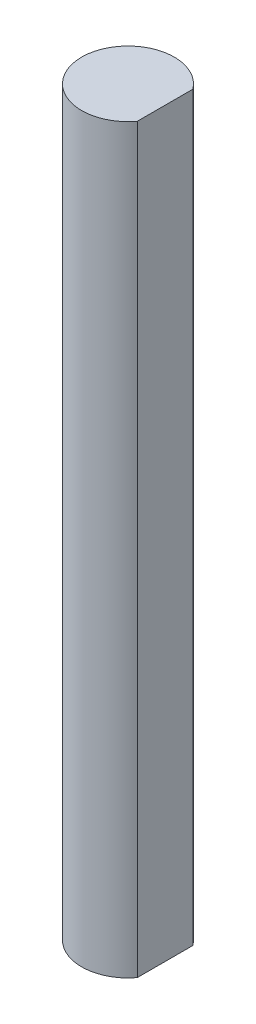
SolidWorks part; units mm, degrees
ref_plane "Front Plane" through (0, 0, 0) normal (0, 0, 1) x (1, 0, 0)
ref_plane "Top Plane" through (0, 0, 0) normal (0, 1, 0) x (1, 0, 0)
ref_plane "Right Plane" through (0, 0, 0) normal (1, 0, 0) x (0, 0, -1)
sketch "Sketch1" plane through (0, 0, 0) normal (0, 1, 0) x (1, 0, 0)
  line L0 (0, 0) -> (2.54, 0) construction
  line L1 (2.54, 3.81) -> (2.54, -3.81)
  circle A0 centre (0, 0) radius 3.175
  point P6 (2.54, 0)
  dimension "D1" = 6.35
  dimension "D2" = 2.54
  dimension "D3" = 7.62
extrude "Boss-Extrude1" add sketch "Sketch1" along normal blind 50.8
equation "\"D2@Sketch1\"=.125-.025"
